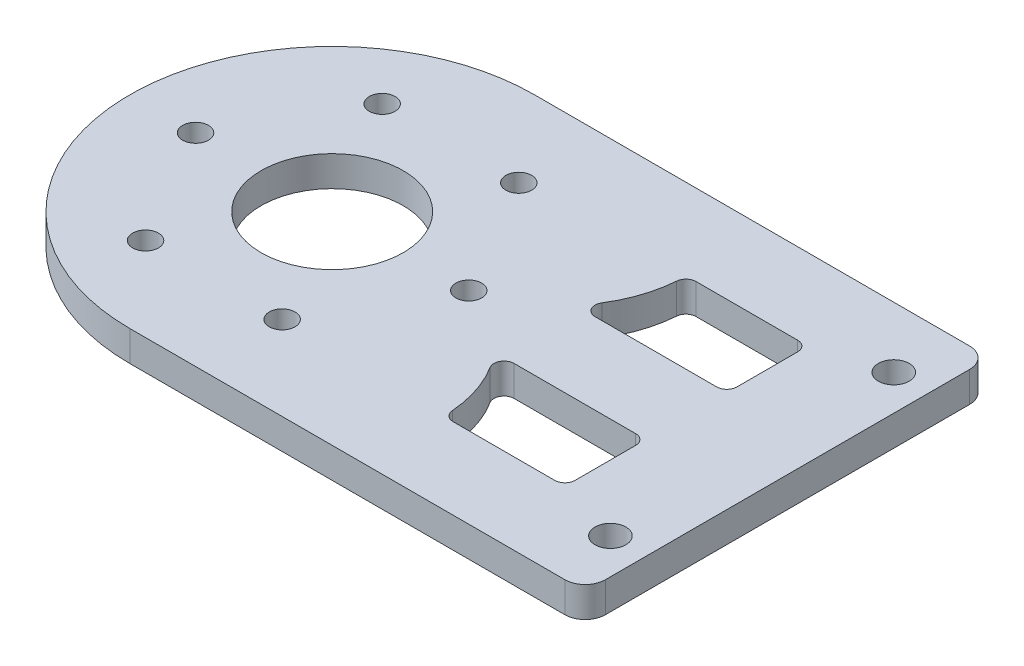
SolidWorks part; units mm, degrees
material "Thornel Mat VMA"
ref_plane "前视基准面" through (0, 0, 0) normal (0, 0, 1) x (1, 0, 0)
ref_plane "上视基准面" through (0, 0, 0) normal (0, 1, 0) x (1, 0, 0)
ref_plane "右视基准面" through (0, 0, 0) normal (1, 0, 0) x (0, 0, -1)
other "Configuration Table"
sketch "草图1" plane through (0, 0, 0) normal (0, 1, 0) x (1, 0, 0)
  line L1 (-22.5, -20) -> (22.5, -20)
  line L2 (-22.5, -20) -> (-22.5, 20)
  line L3 (-22.5, 20) -> (22.5, 20)
  line L4 (22.5, -20) -> (22.5, 20)
  line L5 (-22.5, -20) -> (22.5, 20) construction
  line L6 (-22.5, 20) -> (22.5, -20) construction
  circle A0 centre (-22.5, 0) radius 20
  point P0 (0, 0)
  dimension "D1" = 40
  dimension "D2" = 45
extrude "凸台-拉伸1" add sketch "草图1" along normal blind 3 contours A0 L1 L4 L3
sketch "草图3" plane through (0, 0, 0) normal (0, 1, 0) x (1, 0, 0)
  circle A0 centre (-22.5, 0) radius 13.5 construction
  circle A1 centre (-36, 0) radius 1.275
  circle A2 centre (-29.25, 11.6913) radius 1.275
  circle A3 centre (-15.75, 11.6913) radius 1.275
  circle A4 centre (-9, 0) radius 1.275
  circle A5 centre (-15.75, -11.6913) radius 1.275
  circle A6 centre (-29.25, -11.6913) radius 1.275
  point P17 (-22.5, 0)
  dimension "D1" = 27
  dimension "D2" = 2.55
  dimension "D3" = 6
extrude "切除-拉伸3" cut sketch "草图3" along normal through all
sketch "草图6" plane through (0, 3, 0) normal (0, 1, 0) x (1, 0, 0)
  circle A0 centre (-22.5, 0) radius 7.025
  arc A1 (-22.5, 20) -> (-22.5, -20) centre (-22.5, 0) ccw construction
  dimension "D1" = 14.05
extrude "切除-拉伸6" cut sketch "草图6" against normal through all
fillet "圆角1" radius 2 2 edges at (22.5, 1.5, 20) (22.5, 1.5, -20)
sketch "草图7" plane through (0, 3, 0) normal (0, 1, 0) x (1, 0, 0)
  line L0 (22.5, -18) -> (22.5, 18) construction
  line L1 (0, 0) -> (22.5, 0) construction
  circle A2 centre (19, -14) radius 1.525
  circle A3 centre (19, 14) radius 1.525
  dimension "D1" = 3.5
  dimension "D2" = 3.05
  dimension "D3" = 28
extrude "切除-拉伸7" cut sketch "草图7" against normal through all
sketch "草图8" plane through (0, 3, 0) normal (0, 1, 0) x (1, 0, 0)
  line L0 (-0.5149, -4) -> (11.5, -4) construction
  line L1 (12.5, -5) -> (12.5, -11) construction
  line L2 (11.5, -12) -> (1.462, -12) construction
  line L3 (-0.5149, -4) -> (11.5, -4)
  line L4 (12.5, -5) -> (12.5, -11)
  line L5 (11.5, -12) -> (1.462, -12)
  arc A1 (0.4649, -11.0759) -> (1.462, -12) centre (1.462, -11) ccw construction
  arc A2 (-0.5149, -4) -> (-1.3619, -5.5316) centre (-0.5149, -5) ccw construction
  arc A3 (12.5, -5) -> (11.5, -4) centre (11.5, -5) ccw construction
  arc A4 (11.5, -12) -> (12.5, -11) centre (11.5, -11) ccw construction
  arc A5 (0.4649, -11.0759) -> (1.462, -12) centre (1.462, -11) ccw
  arc A6 (-0.5149, -4) -> (-1.3619, -5.5316) centre (-0.5149, -5) ccw
  arc A7 (12.5, -5) -> (11.5, -4) centre (11.5, -5) ccw
  arc A8 (11.5, -12) -> (12.5, -11) centre (11.5, -11) ccw
  arc A9 (0.4649, -11.0759) -> (-1.3619, -5.5316) centre (-11.6667, -12) ccw construction
  arc A10 (0.4649, -11.0759) -> (-1.3619, -5.5316) centre (-11.6667, -12) ccw
extrude "切除-拉伸8" cut sketch "草图8" against normal blind 10
mirror "镜向1" about plane through (0, 0, 0) normal (0, 0, 1) of "切除-拉伸8"
